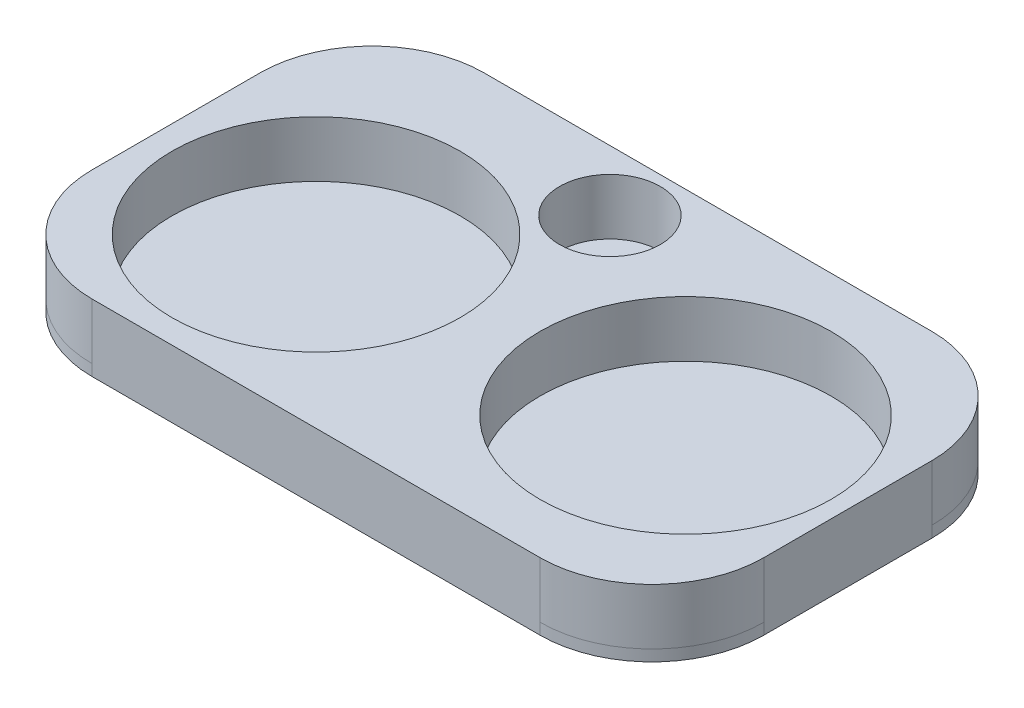
SolidWorks part; units mm, degrees
ref_plane "Front Plane" through (0, 0, 0) normal (0, 0, 1) x (1, 0, 0)
ref_plane "Top Plane" through (0, 0, 0) normal (0, 1, 0) x (1, 0, 0)
ref_plane "Right Plane" through (0, 0, 0) normal (1, 0, 0) x (0, 0, -1)
sketch "Sketch1" plane through (0, 0, 0) normal (0, 1, 0) x (1, 0, 0)
  line L5 (-30.5438, 5.5068) -> (89.4562, 5.5068)
  line L6 (-30.5438, 5.5068) -> (-30.5438, -64.4932)
  line L13 (-30.5438, -64.4932) -> (89.4562, -64.4932)
  line L14 (89.4562, 5.5068) -> (89.4562, -64.4932)
  line L15 (29.4562, -64.4932) -> (29.4562, 5.5068) construction
  line L16 (-30.5438, -29.4932) -> (89.4562, -29.4932) construction
  circle A0 centre (-0.5438, -34.4932) radius 25.75
  circle A1 centre (22.7752, -5.3211) radius 9
  circle A2 centre (60.4562, -29.4932) radius 26
  point P6 (59.8968, -27.3554)
  point P7 (25.6102, -5.2105)
  point P8 (-1.1032, -35.0676)
  point P9 (0, 0)
  point P12 (22.7752, -5.3211)
  point P16 (2.1179, -64.4932)
  point P150 (-29.3905, -26.0855)
  point P208 (-1.1032, -29.4932)
  point P223 (29.4562, -29.4932)
  dimension "D3" = 51.5
  dimension "D4" = 51.5
  dimension "D7" = 18
  dimension "D5" = 52
  dimension "D6" = 61
  dimension "D1" = 70
  dimension "D2" = 120
  dimension "D8" = 70
  dimension "D9" = 30
  dimension "D10" = 30
extrude "Boss-Extrude3" add sketch "Sketch1" along normal blind 12
fillet "Fillet1" radius 20 4 edges at (89.4562, 6, -5.5068) (89.4562, 6, 64.4932) (-30.5438, 6, -5.5068) (-30.5438, 6, 64.4932)
sketch "Sketch4" plane through (0, 0, 0) normal (0, 1, 0) x (1, 0, 0)
  line L0 (-10.5438, -64.4932) -> (69.4562, -64.4932) construction
  line L1 (-30.5438, 5.5068) -> (89.4562, 5.5068)
  line L2 (-30.5438, 5.5068) -> (-30.5438, -64.4932)
  line L3 (-30.5438, -64.4932) -> (89.4562, -64.4932)
  line L4 (89.4562, 5.5068) -> (89.4562, -64.4932)
  line L5 (29.4562, -64.4932) -> (29.4562, 5.5068) construction
  line L6 (-30.5438, -29.4932) -> (89.4562, -29.4932) construction
  line L7 (-30.5438, -14.4932) -> (-30.5438, -44.4932) construction
  line L8 (89.4562, -44.4932) -> (89.4562, -14.4932) construction
  line L9 (69.4562, 5.5068) -> (-10.5438, 5.5068) construction
  point P668 (29.4562, -29.4932)
extrude "Boss-Extrude4" add sketch "Sketch4" along normal blind 2
fillet "Fillet3" radius 20 4 edges at (89.4562, 1, -5.5068) (89.4562, 1, 64.4932) (-30.5438, 1, 64.4932) (-30.5438, 1, -5.5068)
